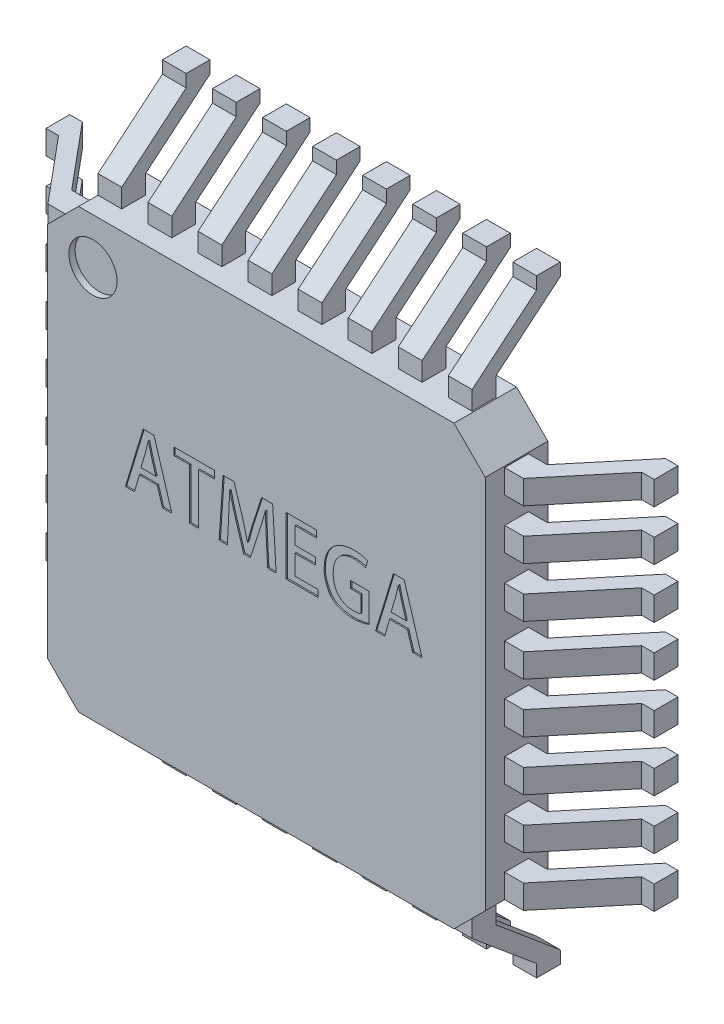
SolidWorks part; units mm, degrees
ref_plane "Plan de face" through (0, 0, 0) normal (0, 0, 1) x (1, 0, 0)
ref_plane "Plan de dessus" through (0, 0, 0) normal (0, 1, 0) x (1, 0, 0)
ref_plane "Plan de droite" through (0, 0, 0) normal (1, 0, 0) x (0, 0, -1)
sketch "Esquisse1" plane through (0, 0, 0) normal (0, 0, 1) x (1, 0, 0)
  line L0 (-6.4232, 0) -> (8.5456, 0) construction
  line L1 (0, -6.4764) -> (0, 6.8796) construction
  line L2 (-3.5, 3) -> (-3, 3.5)
  line L3 (-3, 3.5) -> (3, 3.5)
  line L4 (-3.5, 3) -> (-3.5, -3)
  line L5 (-3, -3.5) -> (3, -3.5)
  line L6 (3.5, 3) -> (3.5, -3)
  line L7 (3, 3.5) -> (3.5, 3)
  line L8 (3, -3.5) -> (3.5, -3)
  line L9 (-3.5, -3) -> (-3, -3.5)
  point P5 (-3.5, 3.5)
  point P6 (3.5, -3.5)
  point P7 (-3.5, -3.5)
  point P8 (3.5, 3.5)
  dimension "D1" = 7
  dimension "D2" = 7
extrude "Corps" add sketch "Esquisse1" along normal blind 1
sketch "Esquisse2" plane through (0, 0, 1) normal (0, 0, 1) x (1, 0, 0)
  line L0 (3, 3.5) -> (-3, 3.5) construction
  line L2 (-3.5, 3) -> (-3.5, -3) construction
  circle A0 centre (-2.77, 2.77) radius 0.385
  dimension "D3" = 0.77
  dimension "D1" = 0.73
  dimension "D2" = 0.73
extrude "Enlèv. mat.-Extru.1" cut sketch "Esquisse2" against normal blind 0.1
sketch "Esquisse3" plane through (0, 0, 1) normal (0, 0, 1) x (1, 0, 0)
  text T0 "ATMEGA" font "@Adobe Heiti Std R" height in points 3
extrude "Texte" cut sketch "Esquisse3" against normal blind 0.02
ref_plane "Plan1" through (0, -3, 0) normal (0, -1, 0) x (-1, 0, 0)
sketch "Esquisse5" plane through (0, -3, 0) normal (0, -1, 0) x (-1, 0, 0)
  line L0 (3.5, -0.69) -> (3.8, -0.69)
  line L1 (3.5, -1) -> (3.5, 0) construction
  line L2 (3.8, -0.69) -> (4.66, 0.34)
  line L3 (4.66, 0.34) -> (4.86, 0.34)
  line L4 (4.86, 0.34) -> (4.86, 0.72)
  line L5 (4.86, 0.72) -> (4.66, 0.72)
  line L6 (3.5, -1) -> (3, -1) construction
  line L7 (3.5, -0.69) -> (3.5, -0.31)
  line L8 (3.5, -0.31) -> (3.8, -0.31)
  line L9 (3.8, -0.31) -> (4.66, 0.72)
  dimension "D1" = 0.3
  dimension "D2" = 0.86
  dimension "D3" = 0.2
  dimension "D4" = 0.38
  dimension "D5" = 0.31
  dimension "D6" = 1.03
  dimension "D7" = 0.2
  dimension "D8" = 0.38
  dimension "D9" = 0.3
extrude "Patte" add sketch "Esquisse5" against normal blind 0.38
pattern_linear "Répétition linéaire1" count 8 spacing 0.8 along (0, 1, 0) of "Patte"
mirror "Symétrie1" about plane through (0, 0, 0) normal (1, 0, 0) of "Répétition linéaire1", "Patte"
ref_plane "Plan2" through (-3, 0, 0) normal (-1, 0, 0) x (0, 0, 1)
sketch "Esquisse6" plane through (-3, 0, 0) normal (-1, 0, 0) x (0, 0, 1)
  line L0 (0.69, -3.5) -> (0.69, -3.8)
  line L1 (1, -3.5) -> (0, -3.5) construction
  line L2 (0.69, -3.8) -> (-0.34, -4.66)
  line L3 (-0.34, -4.66) -> (-0.34, -4.86)
  line L4 (-0.34, -4.86) -> (-0.72, -4.86)
  line L5 (-0.72, -4.86) -> (-0.72, -4.66)
  line L6 (-0.72, -4.66) -> (0.31, -3.8)
  line L7 (0.31, -3.8) -> (0.31, -3.5)
  line L8 (0.31, -3.5) -> (0.69, -3.5)
  line L9 (1, -3) -> (1, -3.5) construction
  dimension "D1" = 0.31
  dimension "D2" = 0.38
  dimension "D3" = 0.3
  dimension "D4" = 0.3
  dimension "D5" = 0.86
  dimension "D6" = 0.2
  dimension "D7" = 1.03
  dimension "D8" = 0.38
  dimension "D9" = 0.2
extrude "Boss.-Extru.3" add sketch "Esquisse6" against normal blind 0.38
pattern_linear "Répétition linéaire2" count 8 spacing 0.8 along (1, 0, 0) of "Boss.-Extru.3"
mirror "Symétrie2" about plane through (0, 0, 0) normal (0, 1, 0) of "Répétition linéaire2", "Boss.-Extru.3"
